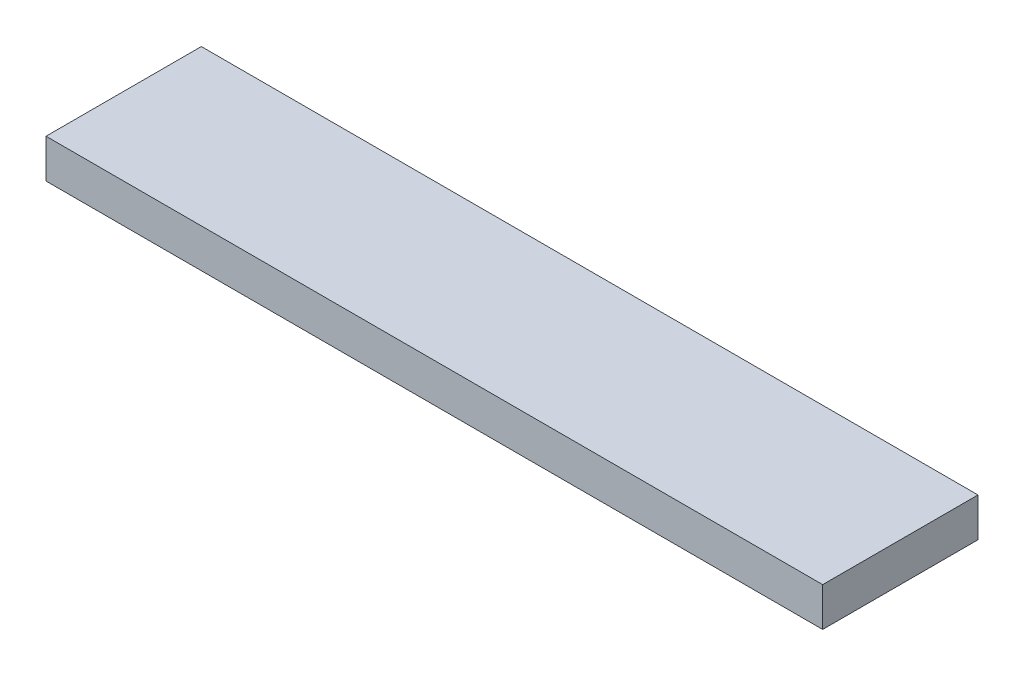
SolidWorks part; units mm, degrees
material "有机玻璃 (TM) GS 丙烯酸铸钣"
ref_plane "前视基准面" through (0, 0, 0) normal (0, 0, 1) x (1, 0, 0)
ref_plane "上视基准面" through (0, 0, 0) normal (0, 1, 0) x (1, 0, 0)
ref_plane "右视基准面" through (0, 0, 0) normal (1, 0, 0) x (0, 0, -1)
sketch "草图1" plane through (0, 15, 0) normal (0, 1, 0) x (1, 0, 0)
  line L1 (-23.2793, 5.6802) -> (76.7207, 5.6802)
  line L2 (-23.2793, 5.6802) -> (-23.2793, -14.3198)
  line L3 (-23.2793, -14.3198) -> (76.7207, -14.3198)
  line L4 (76.7207, 5.6802) -> (76.7207, -14.3198)
extrude "凸台-拉伸1" add sketch "草图1" along normal blind 5
